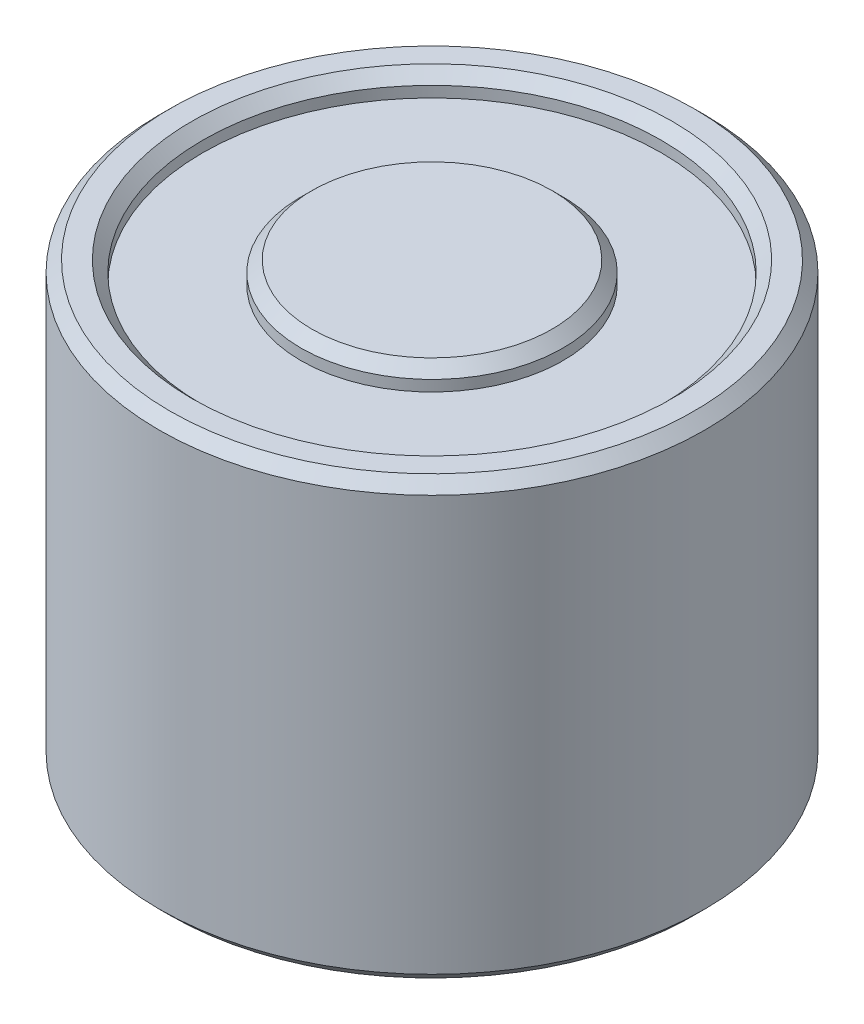
SolidWorks part; units mm, degrees
ref_plane "Спереди" through (0, 0, 0) normal (0, 0, 1) x (1, 0, 0)
ref_plane "Сверху" through (0, 0, 0) normal (0, 1, 0) x (1, 0, 0)
ref_plane "Справа" through (0, 0, 0) normal (1, 0, 0) x (0, 0, -1)
sketch "Эскиз1" plane through (0, 0, 0) normal (0, 1, 0) x (1, 0, 0)
  circle A0 centre (0, 0) radius 12.5
  dimension "D1" = 25
extrude "Бобышка-Вытянуть1" add sketch "Эскиз1" along normal blind 20
sketch "Эскиз2" plane through (0, 20, 0) normal (0, 1, 0) x (1, 0, 0)
  circle A0 centre (0, 0) radius 10.5
  circle A1 centre (0, 0) radius 6
  dimension "D1" = 21
  dimension "D2" = 12
extrude "Вырез-Вытянуть1" cut sketch "Эскиз2" against normal blind 1
chamfer "Фаска1" distance 0.5 angle 45 4 edges at (0, 20, 10.5) (0, 20, 6) (0, 0, 12.5) (0, 20, 12.5)
sketch "Эскиз3" plane through (0, 0, 0) normal (0, -1, 0) x (1, 0, 0)
  circle A0 centre (0, 0) radius 2
  dimension "D1" = 4
extrude "Вырез-Вытянуть2" cut sketch "Эскиз3" against normal blind 12
chamfer "Фаска2" distance 1 angle 45 1 edges at (0, 0, -2)
